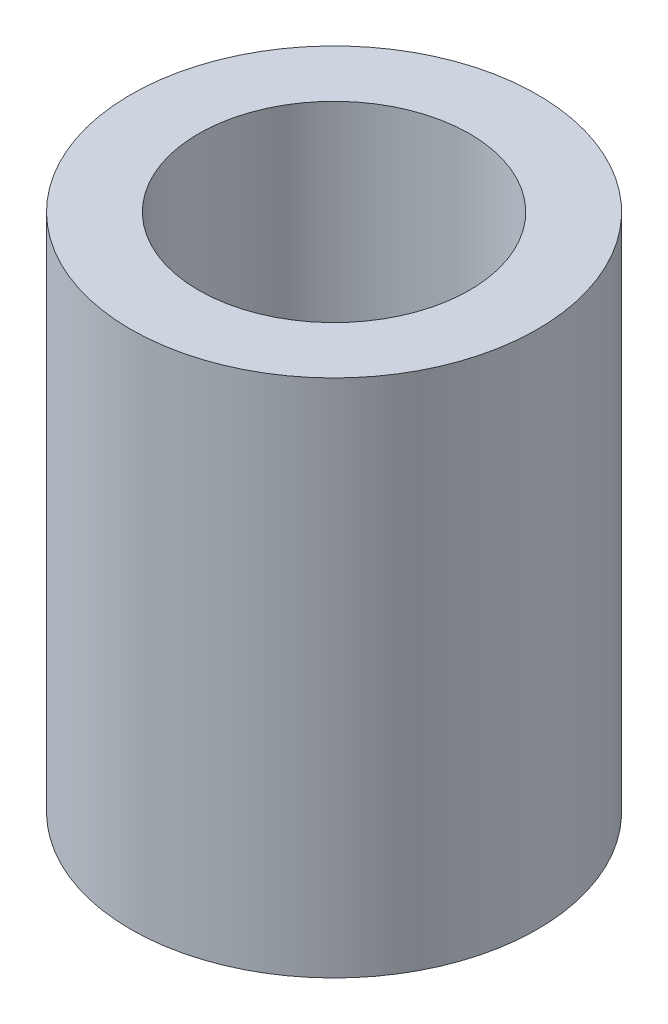
SolidWorks part; units mm, degrees
ref_plane "Front Plane" through (0, 0, 0) normal (0, 0, 1) x (1, 0, 0)
ref_plane "Top Plane" through (0, 0, 0) normal (0, 1, 0) x (1, 0, 0)
ref_plane "Right Plane" through (0, 0, 0) normal (1, 0, 0) x (0, 0, -1)
sketch "Sketch1" plane through (0, 0, 0) normal (0, 1, 0) x (1, 0, 0)
  line L0 (-2.5, 0) -> (-2.5, -3) construction
  line L1 (-0.5, 0) -> (-4.5, 0)
  line L2 (0, -0.5) -> (0, -2.5)
  line L3 (-0.5, -3) -> (-4.5, -3)
  line L4 (-5, -0.5) -> (-5, -2.5)
  arc A0 (-4.5, -3) -> (-5, -2.5) centre (-4.5, -2.5) cw
  arc A1 (0, -2.5) -> (-0.5, -3) centre (-0.5, -2.5) cw
  arc A2 (-0.5, 0) -> (0, -0.5) centre (-0.5, -0.5) cw
  arc A3 (-5, -0.5) -> (-4.5, 0) centre (-4.5, -0.5) cw
  circle A4 centre (-2.5, -1.5) radius 4.5
  point P7 (-5, -3)
  point P12 (0, 0)
  point P15 (-5, 0)
  dimension "D3" = 0.5
  dimension "D4" = 9
  dimension "D1" = 5
  dimension "D2" = 3
extrude "Boss-Extrude1" add sketch "Sketch1" along normal blind 5.5
sketch "Sketch2" plane through (0, 5.5, 0) normal (0, 1, 0) x (1, 0, 0)
  line L0 (-2.5, 0) -> (-2.5, -3) construction
  line L1 (-0.5, 0) -> (-4.5, 0) construction
  line L2 (-4.5, -3) -> (-0.5, -3) construction
  circle A0 centre (-2.5, -1.5) radius 4.5
extrude "Boss-Extrude2" add sketch "Sketch2" along normal blind 6
sketch "Sketch3" plane through (0, 11.5, 0) normal (0, 1, 0) x (1, 0, 0)
  circle A0 centre (-2.5, -1.5) radius 3
  dimension "D1" = 6
extrude "Cut-Extrude1" cut sketch "Sketch3" against normal blind 5
